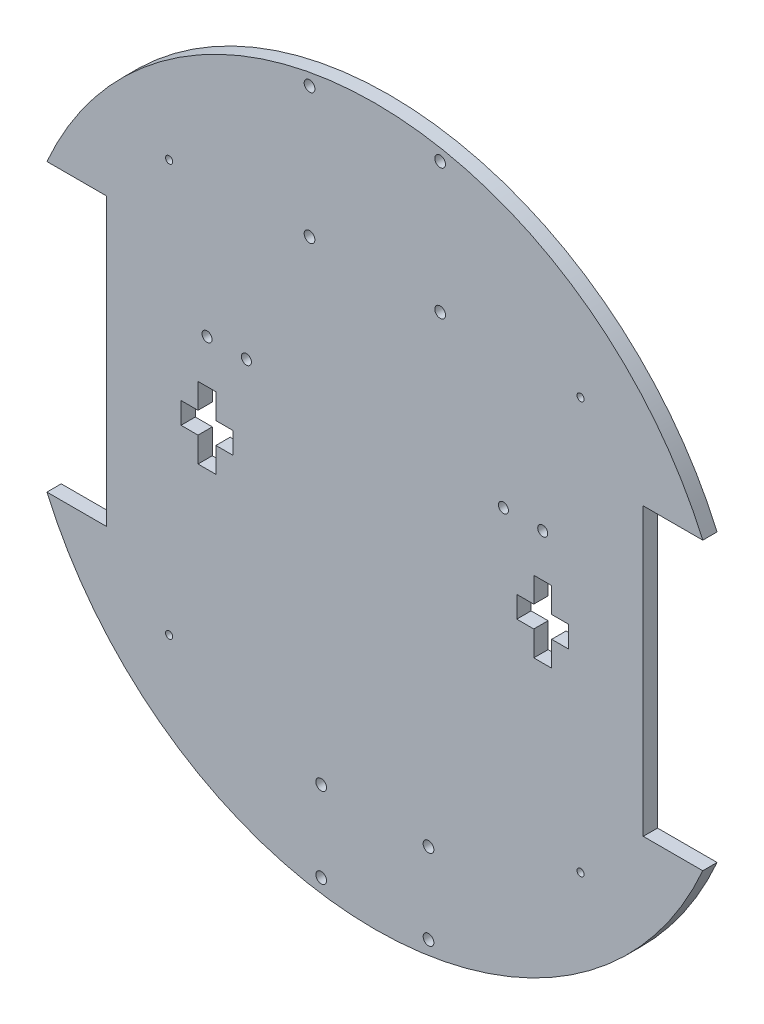
SolidWorks part; units mm, degrees
ref_plane "Plano frontal" through (0, 0, 0) normal (0, 0, 1) x (1, 0, 0)
ref_plane "Plano superior" through (0, 0, 0) normal (0, 1, 0) x (1, 0, 0)
ref_plane "Plano direito" through (0, 0, 0) normal (1, 0, 0) x (0, 0, -1)
sketch "Esboço1" plane through (0, 0, 0) normal (0, 0, 1) x (1, 0, 0)
  line L9 (75.0145, -40) -> (91.6515, -40)
  line L10 (75.0145, 40) -> (91.6515, 40)
  line L11 (-74.9855, -40) -> (-74.9855, 40)
  line L16 (-74.9855, 40) -> (-91.6515, 40)
  line L17 (-74.9855, -40) -> (-91.6515, -40)
  line L18 (75.0145, -40) -> (75.0145, 40)
  line L19 (49.4245, -5.0971) -> (49.4245, -12.0971)
  line L27 (49.4245, 0.9029) -> (49.4245, 7.9029)
  line L29 (49.4245, 7.9029) -> (44.4245, 7.9029)
  line L32 (49.4245, -12.0971) -> (44.4245, -12.0971)
  line L36 (39.6745, 0.9029) -> (39.6745, -5.0971)
  line L40 (39.6745, 0.9029) -> (44.4245, 0.9029)
  line L41 (39.6745, -5.0971) -> (44.4245, -5.0971)
  line L42 (44.4245, -5.0971) -> (44.4245, -12.0971)
  line L43 (44.4245, 7.9029) -> (44.4245, 0.9029)
  line L44 (46.9245, 7.9029) -> (46.9245, -12.0971) construction
  line L45 (54.1745, -5.0971) -> (49.4245, -5.0971)
  line L46 (54.1745, 0.9029) -> (54.1745, -5.0971)
  line L47 (54.1745, 0.9029) -> (49.4245, 0.9029)
  line L49 (-54.1745, 0.9029) -> (-54.1745, -5.0971)
  line L50 (-54.1745, 0.9029) -> (-49.4245, 0.9029)
  line L51 (-49.4245, 0.9029) -> (-49.4245, 7.9029)
  line L52 (-49.4245, 7.9029) -> (-44.4245, 7.9029)
  line L53 (-44.4245, 7.9029) -> (-44.4245, 0.9029)
  line L54 (-39.6745, 0.9029) -> (-44.4245, 0.9029)
  line L55 (-39.6745, 0.9029) -> (-39.6745, -5.0971)
  line L56 (-39.6745, -5.0971) -> (-44.4245, -5.0971)
  line L57 (-44.4245, -5.0971) -> (-44.4245, -12.0971)
  line L58 (-49.4245, -12.0971) -> (-44.4245, -12.0971)
  line L59 (-49.4245, -5.0971) -> (-49.4245, -12.0971)
  line L60 (-54.1745, -5.0971) -> (-49.4245, -5.0971)
  arc A0 (-91.6515, -40) -> (91.6515, -40) centre (0, 0) ccw
  circle A1 centre (-57.5, 57.5) radius 1
  circle A2 centre (57.5, 57.5) radius 1
  circle A3 centre (57.5, -57.5) radius 1
  circle A4 centre (-57.5, -57.5) radius 1
  arc A5 (91.6515, 40) -> (-91.6515, 40) centre (0, 0) ccw
  circle A8 centre (-46.9, 20) radius 1.4
  circle A9 centre (46.9245, 19.9029) radius 1.4
  circle A18 centre (-18.25, 95) radius 1.5
  circle A19 centre (18.25, 95) radius 1.5
  circle A20 centre (18.25, 58.5) radius 1.5
  circle A21 centre (-18.25, 58.5) radius 1.5
  circle A22 centre (-15, -95) radius 1.5
  circle A23 centre (15, -95) radius 1.5
  circle A24 centre (15, -72.5) radius 1.5
  circle A25 centre (-15, -72.5) radius 1.5
  circle A26 centre (-35.9, 20) radius 1.4
  circle A27 centre (35.9245, 20) radius 1.4
  dimension "D1" = 200
  dimension "D4" = 6
  dimension "D3" = 2.8
  dimension "D2" = 2.8
  dimension "D7" = 22.5
extrude "Ressalto-extrusão2" add sketch "Esboço1" along normal blind 4
